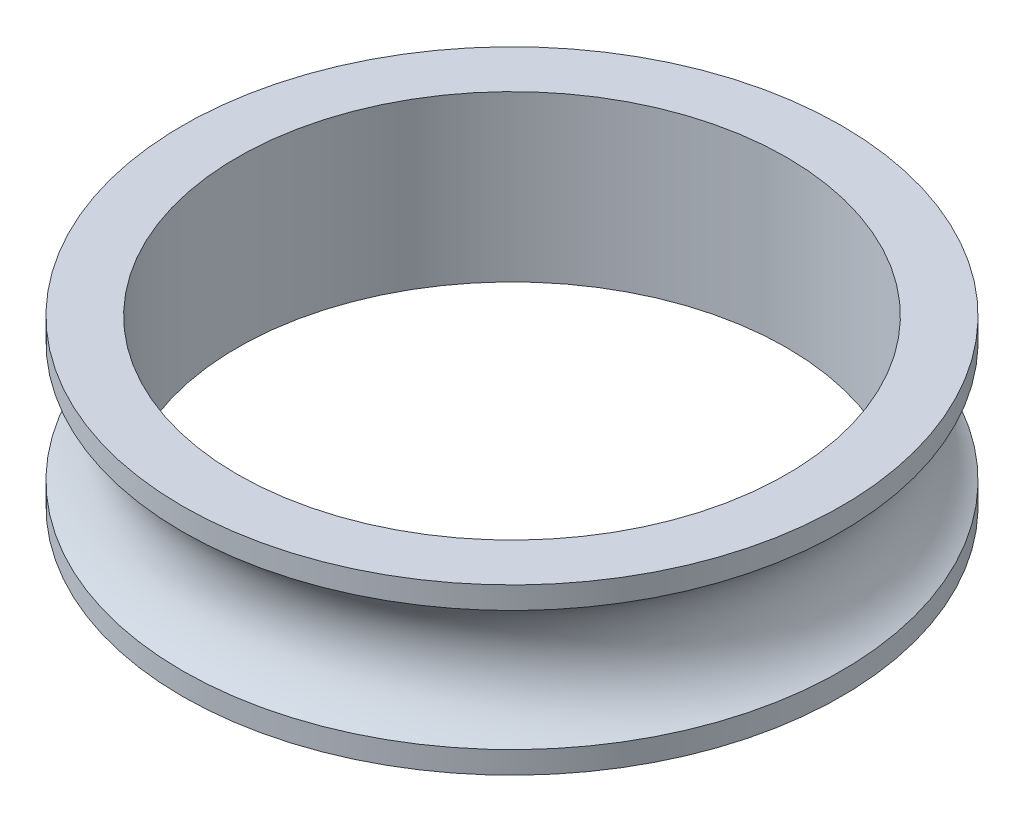
SolidWorks part; units mm, degrees
ref_plane "Front Plane" through (0, 0, 0) normal (0, 0, 1) x (1, 0, 0)
ref_plane "Top Plane" through (0, 0, 0) normal (0, 1, 0) x (1, 0, 0)
ref_plane "Right Plane" through (0, 0, 0) normal (1, 0, 0) x (0, 0, -1)
sketch "Sketch1" plane through (0, 0, 0) normal (0, 1, 0) x (1, 0, 0)
  circle A0 centre (0, 0) radius 10
  circle A1 centre (0, 0) radius 12
  dimension "D1" = 20
  dimension "D2" = 24
extrude "Boss-Extrude1" add sketch "Sketch1" along normal blind 6 contours A0 | A1
sketch "Sketch4" plane through (0, 0, 0) normal (1, 0, 0) x (0, 0, -1)
  line L1 (0, 0) -> (0, 9.2745) construction
  circle A1 centre (-13.2, 3) radius 2.5
  dimension "D1" = 5
  dimension "D2" = 13.2
revolve "Cut-Revolve2" cut sketch "Sketch4" angle 360 about L1
